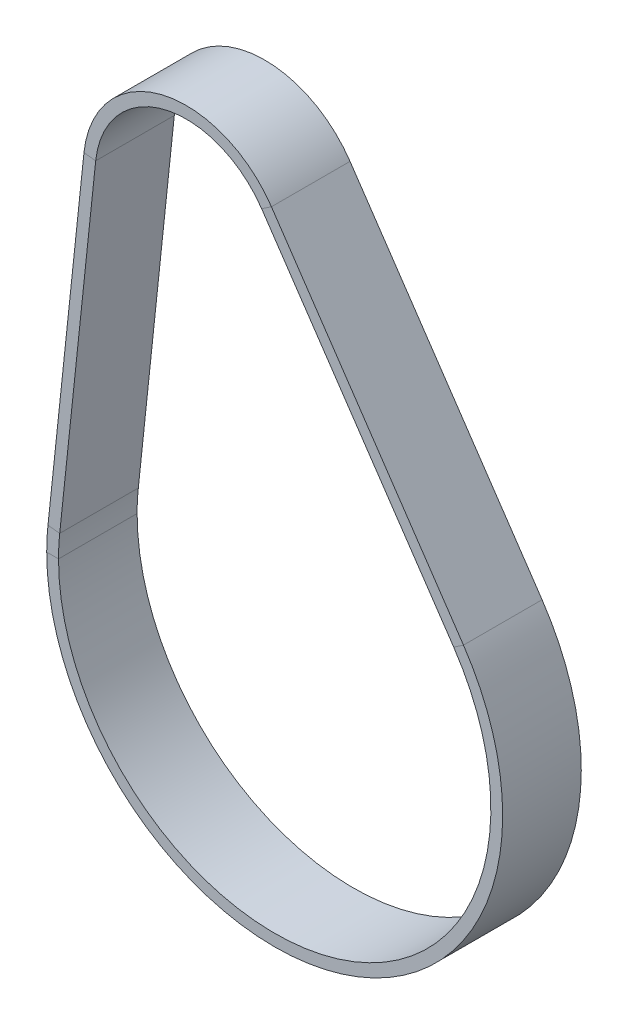
SolidWorks part; units mm, degrees
ref_plane "前视基准面" through (0, 0, 0) normal (0, 0, 1) x (1, 0, 0)
ref_plane "上视基准面" through (0, 0, 0) normal (0, 1, 0) x (1, 0, 0)
ref_plane "右视基准面" through (0, 0, 0) normal (1, 0, 0) x (0, 0, -1)
sketch "草图2" plane through (0, 0, 0) normal (0, 0, 1) x (1, 0, 0)
  line L0 (0, 0) -> (1, 0) construction
  line L1 (0, 0) -> (0, 1) construction
  line L2 (-56.9979, 6.0209) -> (-47.844, 92.6772)
  line L3 (-1.3975, 104.2888) -> (47.4589, 32.1351)
  arc A0 (47.4589, 32.1351) -> (-56.9979, 6.0209) centre (0, 0) cw
  arc A1 (-47.844, 92.6772) -> (-1.3975, 104.2888) centre (-22.5, 90) cw
sketch "草图3" plane through (0, 0, 0) normal (0, 1, 0) x (1, 0, 0)
  line L1 (-55, 10) -> (-58, 10)
  line L2 (-55, 10) -> (-55, -10)
  line L3 (-55, -10) -> (-58, -10)
  line L4 (-58, 10) -> (-58, -10)
  dimension "D1" = 3
  dimension "D2" = 20
  dimension "D3" = 10
  dimension "D4" = 55
sweep "扫描1" add profiles "草图3" path "草图2"
